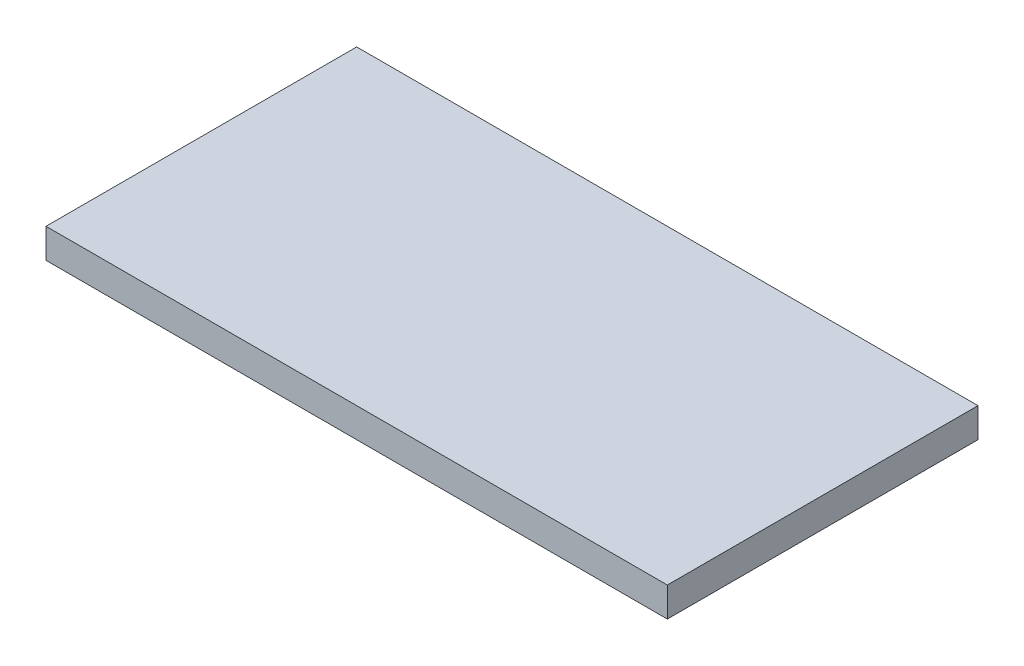
SolidWorks part; units mm, degrees
ref_plane "Front Plane" through (0, 0, 0) normal (0, 0, 1) x (1, 0, 0)
ref_plane "Top Plane" through (0, 0, 0) normal (0, 1, 0) x (1, 0, 0)
ref_plane "Right Plane" through (0, 0, 0) normal (1, 0, 0) x (0, 0, -1)
sketch "Sketch1" plane through (0, 0, 0) normal (0, 1, 0) x (1, 0, 0)
  line L1 (0, 0) -> (400, 0)
  line L2 (0, 0) -> (0, 200)
  line L3 (0, 200) -> (400, 200)
  line L4 (400, 0) -> (400, 200)
  dimension "D1" = 400
  dimension "D2" = 200
extrude "Boss-Extrude1" add sketch "Sketch1" along normal blind 19
sketch "Sketch2" plane through (0, 19, 0) normal (0, 1, 0) x (1, 0, 0)
  line L0 (0, 200) -> (0, 0) construction
  line L1 (0, 180) -> (400, 180)
  line L2 (0, 180) -> (0, 20)
  line L3 (0, 20) -> (400, 20)
  line L4 (400, 180) -> (400, 20)
  line L5 (400, 0) -> (400, 200) construction
  line L6 (400, 200) -> (0, 200) construction
  line L7 (0, 0) -> (400, 0) construction
  dimension "D1" = 160
  dimension "D2" = 20
  dimension "D3" = 20
